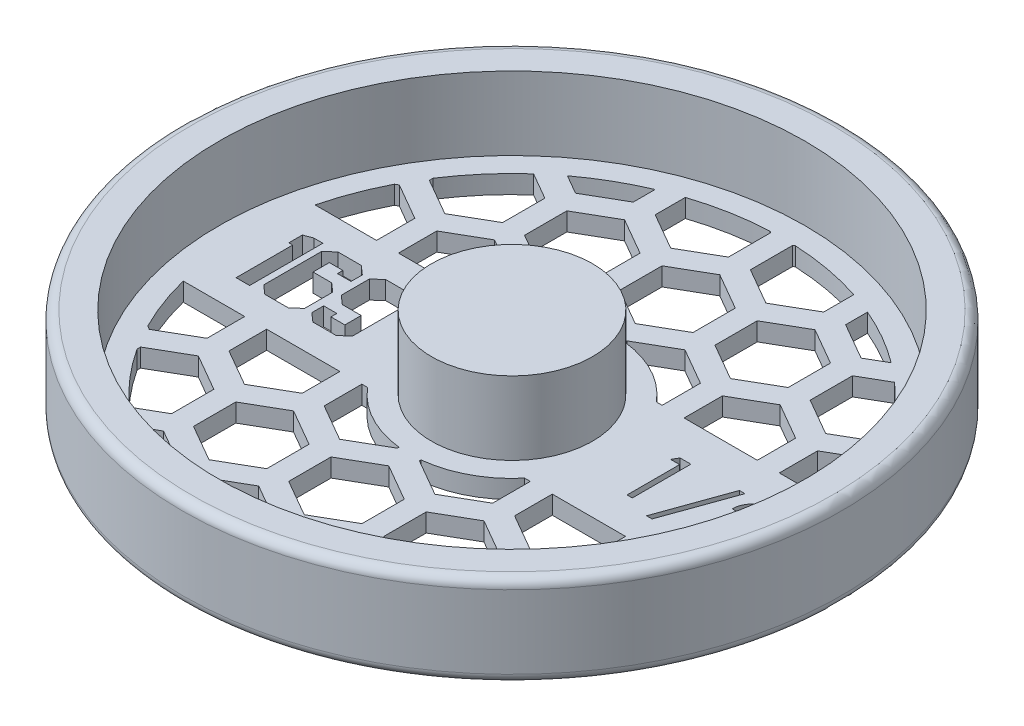
SolidWorks part; units mm, degrees
ref_plane "Front Plane" through (0, 0, 0) normal (0, 0, 1) x (1, 0, 0)
ref_plane "Top Plane" through (0, 0, 0) normal (0, 1, 0) x (1, 0, 0)
ref_plane "Right Plane" through (0, 0, 0) normal (1, 0, 0) x (0, 0, -1)
sketch "Sketch1" plane through (0, 0, 0) normal (0, 0, 1) x (1, 0, 0)
  line L0 (0, 0) -> (0, 15.875)
  line L1 (0, 15.875) -> (13.97, 15.875)
  line L2 (13.97, 15.875) -> (13.97, 3.175)
  line L3 (13.97, 3.175) -> (50.8, 3.175)
  line L4 (50.8, 3.175) -> (50.8, 15.875)
  line L5 (50.8, 15.875) -> (55.5625, 15.875)
  line L6 (57.15, 14.2875) -> (57.15, 1.5875)
  line L7 (55.5625, 0) -> (0, 0)
  arc A0 (55.5625, 0) -> (57.15, 1.5875) centre (55.5625, 1.5875) ccw
  arc A1 (57.15, 14.2875) -> (55.5625, 15.875) centre (55.5625, 14.2875) ccw
  dimension "D7" = 1.5875
  dimension "D1" = 50.8
  dimension "D2" = 3.175
  dimension "D3" = 6.35
  dimension "D4" = 13.97
  dimension "D5" = 12.7
  dimension "D6" = 12.7
revolve "Revolve1" add sketch "Sketch1" angle 360 about L0
sketch "Sketch3" plane through (0, 3.175, 0) normal (0, 1, 0) x (1, 0, 0)
  line L0 (-13.97, 0) -> (-50.8, 0) construction
  line L1 (-13.97, -6.35) -> (-50.8, -6.35) construction
  line L2 (13.97, 0) -> (50.8, 0) construction
  line L3 (13.97, -5.08) -> (50.8, -5.08) construction
  circle A0 centre (0, 0) radius 13.97 construction
  circle A1 centre (0, 0) radius 13.97 construction
  circle A2 centre (0, 0) radius 50.8 construction
  circle A3 centre (0, 0) radius 50.8 construction
  text T0 "169" font "Jersey M54" height 12.7
  text T1 "1/2" font "Century Gothic" height 10.16
  dimension "D1" = 6.35
  dimension "D2" = 5.08
extrude "Cut-Extrude2" cut sketch "Sketch3" against normal through all both and the other way through all
sketch "Sketch4" plane through (0, 3.175, 0) normal (0, 1, 0) x (1, 0, 0)
  line L0 (10.16, -3.6662) -> (16.51, -7.3323)
  line L1 (0, -7.3323) -> (6.35, -3.6662)
  line L2 (6.35, -3.6662) -> (6.35, 3.6662)
  line L3 (6.35, 3.6662) -> (0, 7.3323)
  line L4 (0, 7.3323) -> (-6.35, 3.6662)
  line L5 (-6.35, 3.6662) -> (-6.35, -3.6662)
  line L6 (-6.35, -3.6662) -> (0, -7.3323)
  line L7 (8.255, -21.6304) -> (14.605, -17.9643)
  line L8 (14.605, -17.9643) -> (14.605, -10.6319)
  line L9 (14.605, -10.6319) -> (8.255, -6.9657)
  line L10 (8.255, -6.9657) -> (1.905, -10.6319)
  line L11 (1.905, -10.6319) -> (1.905, -17.9643)
  line L12 (1.905, -17.9643) -> (8.255, -21.6304)
  line L13 (10.16, 3.6662) -> (10.16, -3.6662)
  line L14 (16.51, 7.3323) -> (10.16, 3.6662)
  line L15 (22.86, 3.6662) -> (16.51, 7.3323)
  line L16 (22.86, -3.6662) -> (22.86, 3.6662)
  line L17 (16.51, -7.3323) -> (22.86, -3.6662)
  line L18 (24.765, -21.6304) -> (31.115, -17.9643)
  line L19 (31.115, -17.9643) -> (31.115, -10.6319)
  line L20 (31.115, -10.6319) -> (24.765, -6.9657)
  line L21 (24.765, -6.9657) -> (18.415, -10.6319)
  line L22 (18.415, -10.6319) -> (18.415, -17.9643)
  line L23 (18.415, -17.9643) -> (24.765, -21.6304)
  line L24 (26.67, -3.6662) -> (33.02, -7.3323)
  line L25 (26.67, 3.6662) -> (26.67, -3.6662)
  line L26 (33.02, 7.3323) -> (26.67, 3.6662)
  line L27 (39.37, 3.6662) -> (33.02, 7.3323)
  line L28 (39.37, -3.6662) -> (39.37, 3.6662)
  line L29 (33.02, -7.3323) -> (39.37, -3.6662)
  line L30 (41.275, -21.6304) -> (47.625, -17.9643)
  line L31 (47.625, -17.9643) -> (47.625, -10.6319)
  line L32 (47.625, -10.6319) -> (41.275, -6.9657)
  line L33 (41.275, -6.9657) -> (34.925, -10.6319)
  line L34 (34.925, -10.6319) -> (34.925, -17.9643)
  line L35 (34.925, -17.9643) -> (41.275, -21.6304)
  line L36 (43.18, -3.6662) -> (49.53, -7.3323)
  line L37 (43.18, 3.6662) -> (43.18, -3.6662)
  line L38 (49.53, 7.3323) -> (43.18, 3.6662)
  line L39 (55.88, 3.6662) -> (49.53, 7.3323)
  line L40 (55.88, -3.6662) -> (55.88, 3.6662)
  line L41 (49.53, -7.3323) -> (55.88, -3.6662)
  line L42 (57.785, -21.6304) -> (64.135, -17.9643)
  line L43 (64.135, -17.9643) -> (64.135, -10.6319)
  line L44 (64.135, -10.6319) -> (57.785, -6.9657)
  line L45 (57.785, -6.9657) -> (51.435, -10.6319)
  line L46 (51.435, -10.6319) -> (51.435, -17.9643)
  line L47 (51.435, -17.9643) -> (57.785, -21.6304)
  line L48 (-22.86, -3.6662) -> (-16.51, -7.3323)
  line L49 (-22.86, 3.6662) -> (-22.86, -3.6662)
  line L50 (-16.51, 7.3323) -> (-22.86, 3.6662)
  line L51 (-10.16, 3.6662) -> (-16.51, 7.3323)
  line L52 (-10.16, -3.6662) -> (-10.16, 3.6662)
  line L53 (-16.51, -7.3323) -> (-10.16, -3.6662)
  line L54 (-8.255, -21.6304) -> (-1.905, -17.9643)
  line L55 (-1.905, -17.9643) -> (-1.905, -10.6319)
  line L56 (-1.905, -10.6319) -> (-8.255, -6.9657)
  line L57 (-8.255, -6.9657) -> (-14.605, -10.6319)
  line L58 (-14.605, -10.6319) -> (-14.605, -17.9643)
  line L59 (-14.605, -17.9643) -> (-8.255, -21.6304)
  line L60 (-39.37, -3.6662) -> (-33.02, -7.3323)
  line L61 (-39.37, 3.6662) -> (-39.37, -3.6662)
  line L62 (-33.02, 7.3323) -> (-39.37, 3.6662)
  line L63 (-26.67, 3.6662) -> (-33.02, 7.3323)
  line L64 (-26.67, -3.6662) -> (-26.67, 3.6662)
  line L65 (-33.02, -7.3323) -> (-26.67, -3.6662)
  line L66 (-24.765, -21.6304) -> (-18.415, -17.9643)
  line L67 (-18.415, -17.9643) -> (-18.415, -10.6319)
  line L68 (-18.415, -10.6319) -> (-24.765, -6.9657)
  line L69 (-24.765, -6.9657) -> (-31.115, -10.6319)
  line L70 (-31.115, -10.6319) -> (-31.115, -17.9643)
  line L71 (-31.115, -17.9643) -> (-24.765, -21.6304)
  line L72 (-55.88, -3.6662) -> (-49.53, -7.3323)
  line L73 (-55.88, 3.6662) -> (-55.88, -3.6662)
  line L74 (-49.53, 7.3323) -> (-55.88, 3.6662)
  line L75 (-43.18, 3.6662) -> (-49.53, 7.3323)
  line L76 (-43.18, -3.6662) -> (-43.18, 3.6662)
  line L77 (-49.53, -7.3323) -> (-43.18, -3.6662)
  line L78 (-41.275, -21.6304) -> (-34.925, -17.9643)
  line L79 (-34.925, -17.9643) -> (-34.925, -10.6319)
  line L80 (-34.925, -10.6319) -> (-41.275, -6.9657)
  line L81 (-41.275, -6.9657) -> (-47.625, -10.6319)
  line L82 (-47.625, -10.6319) -> (-47.625, -17.9643)
  line L83 (-47.625, -17.9643) -> (-41.275, -21.6304)
  line L84 (-6.35, 25.0358) -> (0, 21.3697)
  line L85 (-6.35, 32.3682) -> (-6.35, 25.0358)
  line L86 (0, 36.0343) -> (-6.35, 32.3682)
  line L87 (6.35, 32.3682) -> (0, 36.0343)
  line L88 (6.35, 25.0358) -> (6.35, 32.3682)
  line L89 (0, 21.3697) -> (6.35, 25.0358)
  line L90 (8.255, 7.0716) -> (14.605, 10.7377)
  line L91 (14.605, 10.7377) -> (14.605, 18.0701)
  line L92 (14.605, 18.0701) -> (8.255, 21.7363)
  line L93 (8.255, 21.7363) -> (1.905, 18.0701)
  line L94 (1.905, 18.0701) -> (1.905, 10.7377)
  line L95 (1.905, 10.7377) -> (8.255, 7.0716)
  line L96 (-8.255, 7.0716) -> (-1.905, 10.7377)
  line L97 (-1.905, 10.7377) -> (-1.905, 18.0701)
  line L98 (-1.905, 18.0701) -> (-8.255, 21.7363)
  line L99 (-8.255, 21.7363) -> (-14.605, 18.0701)
  line L100 (-14.605, 18.0701) -> (-14.605, 10.7377)
  line L101 (-14.605, 10.7377) -> (-8.255, 7.0716)
  line L102 (-22.86, 25.0358) -> (-16.51, 21.3697)
  line L103 (-16.51, 21.3697) -> (-10.16, 25.0358)
  line L104 (-10.16, 25.0358) -> (-10.16, 32.3682)
  line L105 (-10.16, 32.3682) -> (-16.51, 36.0343)
  line L106 (-16.51, 36.0343) -> (-22.86, 32.3682)
  line L107 (-22.86, 32.3682) -> (-22.86, 25.0358)
  line L108 (-24.765, 7.0716) -> (-18.415, 10.7377)
  line L109 (-18.415, 10.7377) -> (-18.415, 18.0701)
  line L110 (-18.415, 18.0701) -> (-24.765, 21.7363)
  line L111 (-24.765, 21.7363) -> (-31.115, 18.0701)
  line L112 (-31.115, 18.0701) -> (-31.115, 10.7377)
  line L113 (-31.115, 10.7377) -> (-24.765, 7.0716)
  line L114 (-39.37, 25.0358) -> (-33.02, 21.3697)
  line L115 (-33.02, 21.3697) -> (-26.67, 25.0358)
  line L116 (-26.67, 25.0358) -> (-26.67, 32.3682)
  line L117 (-26.67, 32.3682) -> (-33.02, 36.0343)
  line L118 (-33.02, 36.0343) -> (-39.37, 32.3682)
  line L119 (-39.37, 32.3682) -> (-39.37, 25.0358)
  line L120 (-55.88, 25.0358) -> (-49.53, 21.3697)
  line L121 (-49.53, 21.3697) -> (-43.18, 25.0358)
  line L122 (-43.18, 25.0358) -> (-43.18, 32.3682)
  line L123 (-43.18, 32.3682) -> (-49.53, 36.0343)
  line L124 (-49.53, 36.0343) -> (-55.88, 32.3682)
  line L125 (-55.88, 32.3682) -> (-55.88, 25.0358)
  line L126 (-41.275, 7.0716) -> (-34.925, 10.7377)
  line L127 (-34.925, 10.7377) -> (-34.925, 18.0701)
  line L128 (-34.925, 18.0701) -> (-41.275, 21.7363)
  line L129 (-41.275, 21.7363) -> (-47.625, 18.0701)
  line L130 (-47.625, 18.0701) -> (-47.625, 10.7377)
  line L131 (-47.625, 10.7377) -> (-41.275, 7.0716)
  line L132 (10.16, 25.0358) -> (16.51, 21.3697)
  line L133 (16.51, 21.3697) -> (22.86, 25.0358)
  line L134 (22.86, 25.0358) -> (22.86, 32.3682)
  line L135 (22.86, 32.3682) -> (16.51, 36.0343)
  line L136 (16.51, 36.0343) -> (10.16, 32.3682)
  line L137 (10.16, 32.3682) -> (10.16, 25.0358)
  line L138 (24.765, 7.0716) -> (31.115, 10.7377)
  line L139 (31.115, 10.7377) -> (31.115, 18.0701)
  line L140 (31.115, 18.0701) -> (24.765, 21.7363)
  line L141 (24.765, 21.7363) -> (18.415, 18.0701)
  line L142 (18.415, 18.0701) -> (18.415, 10.7377)
  line L143 (18.415, 10.7377) -> (24.765, 7.0716)
  line L144 (26.67, 25.0358) -> (33.02, 21.3697)
  line L145 (33.02, 21.3697) -> (39.37, 25.0358)
  line L146 (39.37, 25.0358) -> (39.37, 32.3682)
  line L147 (39.37, 32.3682) -> (33.02, 36.0343)
  line L148 (33.02, 36.0343) -> (26.67, 32.3682)
  line L149 (26.67, 32.3682) -> (26.67, 25.0358)
  line L150 (41.275, 7.0716) -> (47.625, 10.7377)
  line L151 (47.625, 10.7377) -> (47.625, 18.0701)
  line L152 (47.625, 18.0701) -> (41.275, 21.7363)
  line L153 (41.275, 21.7363) -> (34.925, 18.0701)
  line L154 (34.925, 18.0701) -> (34.925, 10.7377)
  line L155 (34.925, 10.7377) -> (41.275, 7.0716)
  line L156 (43.18, 25.0358) -> (49.53, 21.3697)
  line L157 (49.53, 21.3697) -> (55.88, 25.0358)
  line L158 (55.88, 25.0358) -> (55.88, 32.3682)
  line L159 (55.88, 32.3682) -> (49.53, 36.0343)
  line L160 (49.53, 36.0343) -> (43.18, 32.3682)
  line L161 (43.18, 32.3682) -> (43.18, 25.0358)
  line L162 (57.785, 7.0716) -> (64.135, 10.7377)
  line L163 (64.135, 10.7377) -> (64.135, 18.0701)
  line L164 (64.135, 18.0701) -> (57.785, 21.7363)
  line L165 (57.785, 21.7363) -> (51.435, 18.0701)
  line L166 (51.435, 18.0701) -> (51.435, 10.7377)
  line L167 (51.435, 10.7377) -> (57.785, 7.0716)
  line L168 (-6.35, 53.7378) -> (0, 50.0717)
  line L169 (-6.35, 61.0702) -> (-6.35, 53.7378)
  line L170 (0, 64.7363) -> (-6.35, 61.0702)
  line L171 (6.35, 61.0702) -> (0, 64.7363)
  line L172 (6.35, 53.7378) -> (6.35, 61.0702)
  line L173 (0, 50.0717) -> (6.35, 53.7378)
  line L174 (8.255, 35.7736) -> (14.605, 39.4397)
  line L175 (14.605, 39.4397) -> (14.605, 46.7721)
  line L176 (14.605, 46.7721) -> (8.255, 50.4383)
  line L177 (8.255, 50.4383) -> (1.905, 46.7721)
  line L178 (1.905, 46.7721) -> (1.905, 39.4397)
  line L179 (1.905, 39.4397) -> (8.255, 35.7736)
  line L180 (-8.255, 35.7736) -> (-1.905, 39.4397)
  line L181 (-1.905, 39.4397) -> (-1.905, 46.7721)
  line L182 (-1.905, 46.7721) -> (-8.255, 50.4383)
  line L183 (-8.255, 50.4383) -> (-14.605, 46.7721)
  line L184 (-14.605, 46.7721) -> (-14.605, 39.4397)
  line L185 (-14.605, 39.4397) -> (-8.255, 35.7736)
  line L186 (-22.86, 53.7378) -> (-16.51, 50.0717)
  line L187 (-16.51, 50.0717) -> (-10.16, 53.7378)
  line L188 (-10.16, 53.7378) -> (-10.16, 61.0702)
  line L189 (-10.16, 61.0702) -> (-16.51, 64.7363)
  line L190 (-16.51, 64.7363) -> (-22.86, 61.0702)
  line L191 (-22.86, 61.0702) -> (-22.86, 53.7378)
  line L192 (-24.765, 35.7736) -> (-18.415, 39.4397)
  line L193 (-18.415, 39.4397) -> (-18.415, 46.7721)
  line L194 (-18.415, 46.7721) -> (-24.765, 50.4383)
  line L195 (-24.765, 50.4383) -> (-31.115, 46.7721)
  line L196 (-31.115, 46.7721) -> (-31.115, 39.4397)
  line L197 (-31.115, 39.4397) -> (-24.765, 35.7736)
  line L198 (-39.37, 53.7378) -> (-33.02, 50.0717)
  line L199 (-33.02, 50.0717) -> (-26.67, 53.7378)
  line L200 (-26.67, 53.7378) -> (-26.67, 61.0702)
  line L201 (-26.67, 61.0702) -> (-33.02, 64.7363)
  line L202 (-33.02, 64.7363) -> (-39.37, 61.0702)
  line L203 (-39.37, 61.0702) -> (-39.37, 53.7378)
  line L204 (-55.88, 53.7378) -> (-49.53, 50.0717)
  line L205 (-49.53, 50.0717) -> (-43.18, 53.7378)
  line L206 (-43.18, 53.7378) -> (-43.18, 61.0702)
  line L207 (-43.18, 61.0702) -> (-49.53, 64.7363)
  line L208 (-49.53, 64.7363) -> (-55.88, 61.0702)
  line L209 (-55.88, 61.0702) -> (-55.88, 53.7378)
  line L210 (-41.275, 35.7736) -> (-34.925, 39.4397)
  line L211 (-34.925, 39.4397) -> (-34.925, 46.7721)
  line L212 (-34.925, 46.7721) -> (-41.275, 50.4383)
  line L213 (-41.275, 50.4383) -> (-47.625, 46.7721)
  line L214 (-47.625, 46.7721) -> (-47.625, 39.4397)
  line L215 (-47.625, 39.4397) -> (-41.275, 35.7736)
  line L216 (10.16, 53.7378) -> (16.51, 50.0717)
  line L217 (16.51, 50.0717) -> (22.86, 53.7378)
  line L218 (22.86, 53.7378) -> (22.86, 61.0702)
  line L219 (22.86, 61.0702) -> (16.51, 64.7363)
  line L220 (16.51, 64.7363) -> (10.16, 61.0702)
  line L221 (10.16, 61.0702) -> (10.16, 53.7378)
  line L222 (24.765, 35.7736) -> (31.115, 39.4397)
  line L223 (31.115, 39.4397) -> (31.115, 46.7721)
  line L224 (31.115, 46.7721) -> (24.765, 50.4383)
  line L225 (24.765, 50.4383) -> (18.415, 46.7721)
  line L226 (18.415, 46.7721) -> (18.415, 39.4397)
  line L227 (18.415, 39.4397) -> (24.765, 35.7736)
  line L228 (26.67, 53.7378) -> (33.02, 50.0717)
  line L229 (33.02, 50.0717) -> (39.37, 53.7378)
  line L230 (39.37, 53.7378) -> (39.37, 61.0702)
  line L231 (39.37, 61.0702) -> (33.02, 64.7363)
  line L232 (33.02, 64.7363) -> (26.67, 61.0702)
  line L233 (26.67, 61.0702) -> (26.67, 53.7378)
  line L234 (41.275, 35.7736) -> (47.625, 39.4397)
  line L235 (47.625, 39.4397) -> (47.625, 46.7721)
  line L236 (47.625, 46.7721) -> (41.275, 50.4383)
  line L237 (41.275, 50.4383) -> (34.925, 46.7721)
  line L238 (34.925, 46.7721) -> (34.925, 39.4397)
  line L239 (34.925, 39.4397) -> (41.275, 35.7736)
  line L240 (43.18, 53.7378) -> (49.53, 50.0717)
  line L241 (49.53, 50.0717) -> (55.88, 53.7378)
  line L242 (55.88, 53.7378) -> (55.88, 61.0702)
  line L243 (55.88, 61.0702) -> (49.53, 64.7363)
  line L244 (49.53, 64.7363) -> (43.18, 61.0702)
  line L245 (43.18, 61.0702) -> (43.18, 53.7378)
  line L246 (57.785, 35.7736) -> (64.135, 39.4397)
  line L247 (64.135, 39.4397) -> (64.135, 46.7721)
  line L248 (64.135, 46.7721) -> (57.785, 50.4383)
  line L249 (57.785, 50.4383) -> (51.435, 46.7721)
  line L250 (51.435, 46.7721) -> (51.435, 39.4397)
  line L251 (51.435, 39.4397) -> (57.785, 35.7736)
  line L252 (-6.35, -32.3682) -> (0, -36.0343)
  line L253 (-6.35, -25.0358) -> (-6.35, -32.3682)
  line L254 (0, -21.3697) -> (-6.35, -25.0358)
  line L255 (6.35, -25.0358) -> (0, -21.3697)
  line L256 (6.35, -32.3682) -> (6.35, -25.0358)
  line L257 (0, -36.0343) -> (6.35, -32.3682)
  line L258 (8.255, -50.3324) -> (14.605, -46.6663)
  line L259 (14.605, -46.6663) -> (14.605, -39.3339)
  line L260 (14.605, -39.3339) -> (8.255, -35.6677)
  line L261 (8.255, -35.6677) -> (1.905, -39.3339)
  line L262 (1.905, -39.3339) -> (1.905, -46.6663)
  line L263 (1.905, -46.6663) -> (8.255, -50.3324)
  line L264 (-8.255, -50.3324) -> (-1.905, -46.6663)
  line L265 (-1.905, -46.6663) -> (-1.905, -39.3339)
  line L266 (-1.905, -39.3339) -> (-8.255, -35.6677)
  line L267 (-8.255, -35.6677) -> (-14.605, -39.3339)
  line L268 (-14.605, -39.3339) -> (-14.605, -46.6663)
  line L269 (-14.605, -46.6663) -> (-8.255, -50.3324)
  line L270 (-22.86, -32.3682) -> (-16.51, -36.0343)
  line L271 (-16.51, -36.0343) -> (-10.16, -32.3682)
  line L272 (-10.16, -32.3682) -> (-10.16, -25.0358)
  line L273 (-10.16, -25.0358) -> (-16.51, -21.3697)
  line L274 (-16.51, -21.3697) -> (-22.86, -25.0358)
  line L275 (-22.86, -25.0358) -> (-22.86, -32.3682)
  line L276 (-24.765, -50.3324) -> (-18.415, -46.6663)
  line L277 (-18.415, -46.6663) -> (-18.415, -39.3339)
  line L278 (-18.415, -39.3339) -> (-24.765, -35.6677)
  line L279 (-24.765, -35.6677) -> (-31.115, -39.3339)
  line L280 (-31.115, -39.3339) -> (-31.115, -46.6663)
  line L281 (-31.115, -46.6663) -> (-24.765, -50.3324)
  line L282 (-39.37, -32.3682) -> (-33.02, -36.0343)
  line L283 (-33.02, -36.0343) -> (-26.67, -32.3682)
  line L284 (-26.67, -32.3682) -> (-26.67, -25.0358)
  line L285 (-26.67, -25.0358) -> (-33.02, -21.3697)
  line L286 (-33.02, -21.3697) -> (-39.37, -25.0358)
  line L287 (-39.37, -25.0358) -> (-39.37, -32.3682)
  line L288 (-55.88, -32.3682) -> (-49.53, -36.0343)
  line L289 (-49.53, -36.0343) -> (-43.18, -32.3682)
  line L290 (-43.18, -32.3682) -> (-43.18, -25.0358)
  line L291 (-43.18, -25.0358) -> (-49.53, -21.3697)
  line L292 (-49.53, -21.3697) -> (-55.88, -25.0358)
  line L293 (-55.88, -25.0358) -> (-55.88, -32.3682)
  line L294 (-41.275, -50.3324) -> (-34.925, -46.6663)
  line L295 (-34.925, -46.6663) -> (-34.925, -39.3339)
  line L296 (-34.925, -39.3339) -> (-41.275, -35.6677)
  line L297 (-41.275, -35.6677) -> (-47.625, -39.3339)
  line L298 (-47.625, -39.3339) -> (-47.625, -46.6663)
  line L299 (-47.625, -46.6663) -> (-41.275, -50.3324)
  line L300 (10.16, -32.3682) -> (16.51, -36.0343)
  line L301 (16.51, -36.0343) -> (22.86, -32.3682)
  line L302 (22.86, -32.3682) -> (22.86, -25.0358)
  line L303 (22.86, -25.0358) -> (16.51, -21.3697)
  line L304 (16.51, -21.3697) -> (10.16, -25.0358)
  line L305 (10.16, -25.0358) -> (10.16, -32.3682)
  line L306 (24.765, -50.3324) -> (31.115, -46.6663)
  line L307 (31.115, -46.6663) -> (31.115, -39.3339)
  line L308 (31.115, -39.3339) -> (24.765, -35.6677)
  line L309 (24.765, -35.6677) -> (18.415, -39.3339)
  line L310 (18.415, -39.3339) -> (18.415, -46.6663)
  line L311 (18.415, -46.6663) -> (24.765, -50.3324)
  line L312 (26.67, -32.3682) -> (33.02, -36.0343)
  line L313 (33.02, -36.0343) -> (39.37, -32.3682)
  line L314 (39.37, -32.3682) -> (39.37, -25.0358)
  line L315 (39.37, -25.0358) -> (33.02, -21.3697)
  line L316 (33.02, -21.3697) -> (26.67, -25.0358)
  line L317 (26.67, -25.0358) -> (26.67, -32.3682)
  line L318 (41.275, -50.3324) -> (47.625, -46.6663)
  line L319 (47.625, -46.6663) -> (47.625, -39.3339)
  line L320 (47.625, -39.3339) -> (41.275, -35.6677)
  line L321 (41.275, -35.6677) -> (34.925, -39.3339)
  line L322 (34.925, -39.3339) -> (34.925, -46.6663)
  line L323 (34.925, -46.6663) -> (41.275, -50.3324)
  line L324 (43.18, -32.3682) -> (49.53, -36.0343)
  line L325 (49.53, -36.0343) -> (55.88, -32.3682)
  line L326 (55.88, -32.3682) -> (55.88, -25.0358)
  line L327 (55.88, -25.0358) -> (49.53, -21.3697)
  line L328 (49.53, -21.3697) -> (43.18, -25.0358)
  line L329 (43.18, -25.0358) -> (43.18, -32.3682)
  line L330 (57.785, -50.3324) -> (64.135, -46.6663)
  line L331 (64.135, -46.6663) -> (64.135, -39.3339)
  line L332 (64.135, -39.3339) -> (57.785, -35.6677)
  line L333 (57.785, -35.6677) -> (51.435, -39.3339)
  line L334 (51.435, -39.3339) -> (51.435, -46.6663)
  line L335 (51.435, -46.6663) -> (57.785, -50.3324)
  line L336 (0, -11.43) -> (0, 11.43)
  line L337 (52.0496, 11.43) -> (-52.0496, 11.43)
  line L338 (52.0496, -11.43) -> (-52.0496, -11.43)
  line L339 (-52.0496, 11.43) -> (-52.0496, -11.43)
  line L340 (52.0496, 11.43) -> (52.0496, -11.43)
  circle A0 centre (0, 0) radius 6.35 construction
  circle A1 centre (8.255, -14.2981) radius 6.35 construction
  circle A2 centre (0, 0) radius 46.99
  circle A3 centre (0, 0) radius 17.78
  point P18 (3.175, -5.4993)
  point P345 (0, 0)
  point P348 (0, 11.43)
  point P351 (0, -11.43)
  dimension "D10" = 93.98
  dimension "D11" = 35.56
  dimension "D1" = 12.7
  dimension "D2" = 12.7
  dimension "D3" = 3.81
  dimension "D4" = 1.905
  dimension "D9" = 22.86
  dimension "D5" = 4
  dimension "D6" = 4
  dimension "D7" = 3
  dimension "D8" = 2
extrude "Cut-Extrude4" cut sketch "Sketch4" against normal through all both and the other way through all contours L129 A2 L337 L127 L128 | L337 L109 L110 L111 L112 | L117 A2 L119 L114 L115 L116 | L193 A2 L197 L192 | L106 L107 L102 L103 L104 L105 | L182 A2 L184 L185 L180 L181 | L84 L89 L88 L87 L86 L85 | A3 L97 L98 L99 L100 L337 | A3 L337 L91 L92 L93 L94 | L175 A2 L177 L178 L179 L174 | L136 L137 L132 L133 L134 L135 | L222 A2 L226 L227 | L146 A2 L148 L149 L144 L145 | L337 L139 L140 L141 L142 | L337 A2 L152 L153 L154 | L30 A2 L338 L34 L35 | L19 L338 L22 L23 L18 | A3 L11 L12 L7 L8 L338 | L312 A2 L314 L315 L316 L317 | L310 A2 L308 L309 | L304 L305 L300 L301 L302 L303 | L263 A2 L259 L260 L261 L262 | L252 L257 L256 L255 L254 L253 | L268 A2 L264 L265 L266 L267 | L274 L275 L270 L271 L272 L273 | L279 A2 L277 L278 | L287 A2 L283 L284 L285 L286 | L338 A2 L83 L78 L79 | L67 L338 L70 L71 L66 | A3 L338 L58 L59 L54 L55
